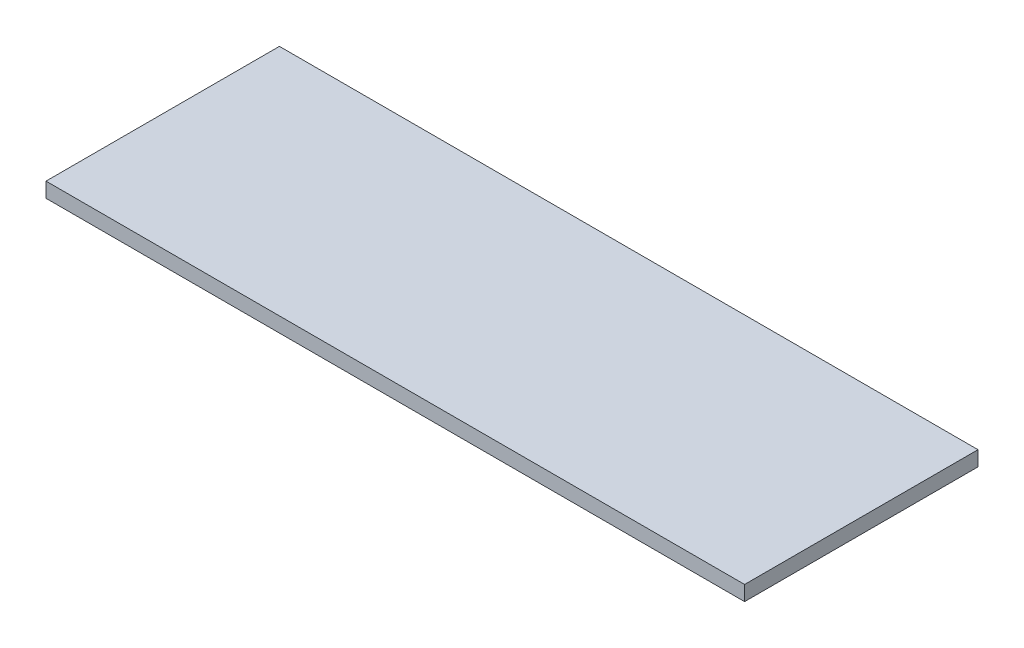
SolidWorks part; units mm, degrees
ref_plane "Спереди" through (0, 0, 0) normal (0, 0, 1) x (1, 0, 0)
ref_plane "Сверху" through (0, 0, 0) normal (0, 1, 0) x (1, 0, 0)
ref_plane "Справа" through (0, 0, 0) normal (1, 0, 0) x (0, 0, -1)
sketch "Эскиз1" plane through (0, 0, 0) normal (0, 1, 0) x (1, 0, 0)
  line L1 (422, -141) -> (-422, -141)
  line L2 (422, -141) -> (422, 141)
  line L3 (422, 141) -> (-422, 141)
  line L4 (-422, -141) -> (-422, 141)
  line L5 (422, -141) -> (-422, 141) construction
  line L6 (422, 141) -> (-422, -141) construction
  point P0 (0, 0)
  dimension "D1" = 282
  dimension "D2" = 844
extrude "Бобышка-Вытянуть1" add sketch "Эскиз1" along normal blind 18
